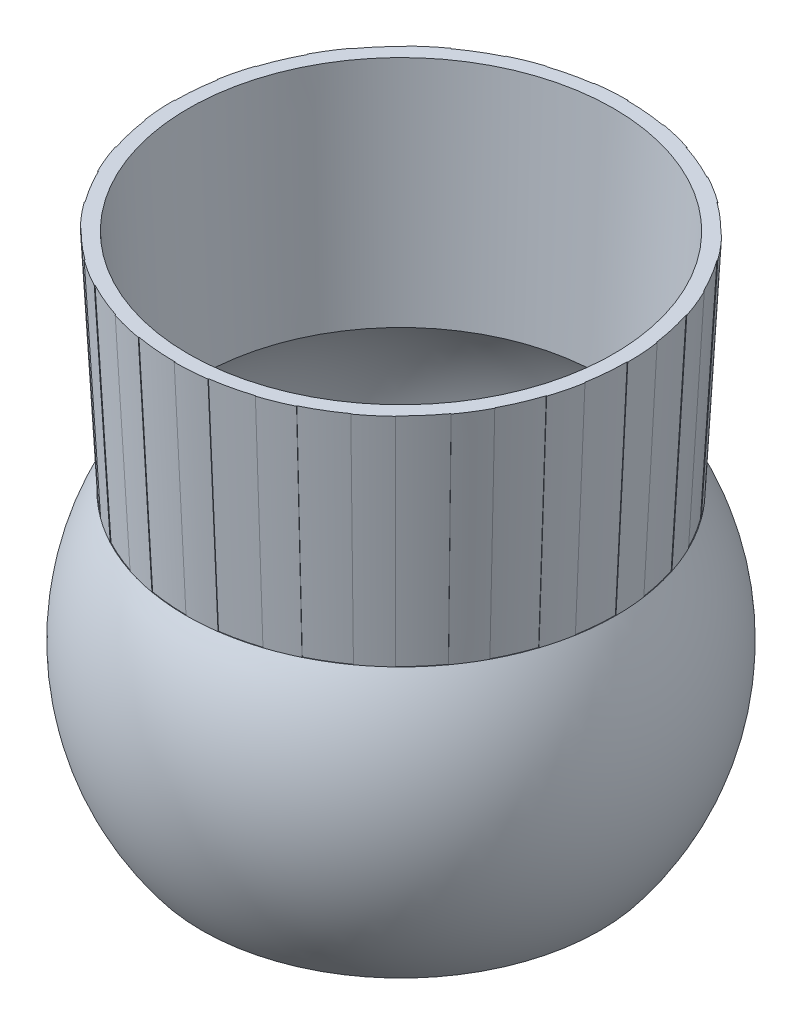
SolidWorks part; units mm, degrees
material "ABS"
ref_plane "Front Plane" through (0, 0, 0) normal (0, 0, 1) x (1, 0, 0)
ref_plane "Top Plane" through (0, 0, 0) normal (0, 1, 0) x (1, 0, 0)
ref_plane "Right Plane" through (0, 0, 0) normal (1, 0, 0) x (0, 0, -1)
sketch "Sketch1" plane through (0, 0, 0) normal (1, 0, 0) x (0, 0, -1)
  line L0 (0, 0) -> (45, 0) construction
  line L1 (0, 50.3555) -> (0, -50.3555) construction
  line L2 (45, 50.3555) -> (45, -50.3555) construction
  line L3 (45, 0) -> (42.5, -47.7028)
  line L4 (40, -105) -> (42.1213, -107.1213)
  line L5 (42.5, -47.7028) -> (45.5, -47.7028) construction
  line L6 (45, 0) -> (48, 0)
  line L7 (48, 0) -> (45.5, -47.7028)
  line L8 (0, -50.3555) -> (0, -113.6539) construction
  arc A2 (42.5, -47.7028) -> (40, -105) centre (0, -74.5516) cw
  arc A3 (45.5, -47.7028) -> (42.1213, -107.1213) centre (0, -74.9209) cw
  point P6 (0, 0)
  point P9 (45, 0)
  point P10 (45, 0)
  dimension "D4" = 50.2703
  dimension "D1" = 45
  dimension "D2" = 40
  dimension "D3" = 42.5
  dimension "D5" = 3
  dimension "D6" = 105
  dimension "D7" = 3
revolve "Revolve1" add sketch "Sketch1" angle 360 about L1
ref_axis "Axis1" through (0, 0, 0) along (0, -1, 0)
sketch "Sketch2" plane through (0, 0, 0) normal (0, 0, 1) x (1, 0, 0)
  line L0 (48, 0) -> (45.5, -47.7028)
  line L1 (48, 0) -> (-48, 0) construction
  line L2 (48, 0) -> (47.8748, 0)
  line L3 (47.8748, 0) -> (45.3748, -47.7028)
  line L4 (45.5, -47.7028) -> (-45.5, -47.7028) construction
  line L5 (45.3748, -47.7028) -> (45.5, -47.7028)
  dimension "D1" = 0.125
revolve "Cut-Revolve1" cut sketch "Sketch2" angle 10 about axis through (0, 0, 0) along (0, -1, 0)
pattern_circular "CirPattern1" count 20 over 360 about axis through (0, 0, 0) along (0, 1, 0) of "Cut-Revolve1"
